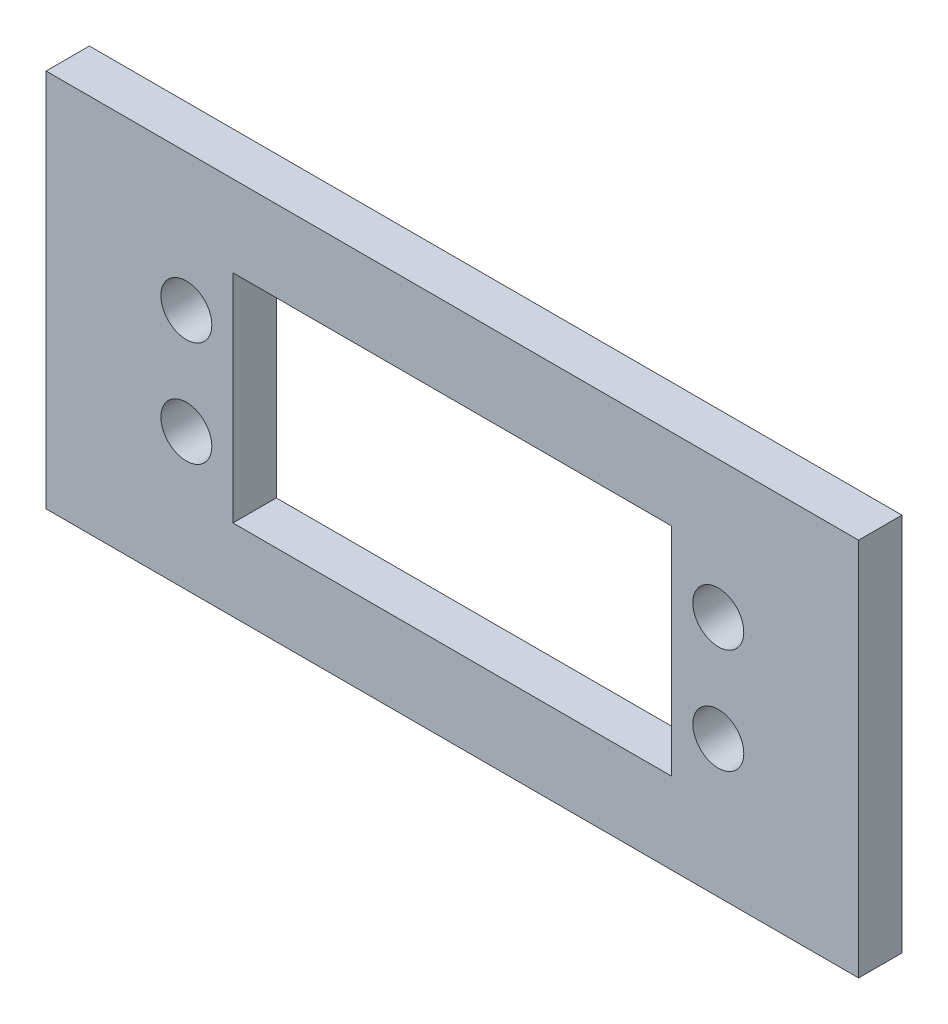
SolidWorks part; units mm, degrees
ref_plane "Front Plane" through (0, 0, 0) normal (0, 0, 1) x (1, 0, 0)
ref_plane "Top Plane" through (0, 0, 0) normal (0, 1, 0) x (1, 0, 0)
ref_plane "Right Plane" through (0, 0, 0) normal (1, 0, 0) x (0, 0, -1)
sketch "Sketch1" plane through (0, 0, 0) normal (0, 0, 1) x (1, 0, 0)
  line L5 (-24.55, 0) -> (-37.5, 0) construction
  line L6 (-24.55, 4.85) -> (24.55, 4.85) construction
  line L14 (-24.55, 4.85) -> (-24.55, -4.85) construction
  line L15 (-24.55, -4.85) -> (24.55, -4.85) construction
  line L16 (24.55, 4.85) -> (24.55, -4.85) construction
  line L17 (-24.55, 4.85) -> (24.55, -4.85) construction
  line L18 (-24.55, -4.85) -> (24.55, 4.85) construction
  line L19 (0, 4.85) -> (0, 32.122) construction
  line L20 (-20.25, 10) -> (20.25, 10)
  line L21 (-20.25, 10) -> (-20.25, -10)
  line L22 (-20.25, -10) -> (20.25, -10)
  line L23 (-37.5, 17.5) -> (37.5, 17.5)
  line L24 (-37.5, 17.5) -> (-37.5, -17.5)
  line L25 (20.25, 10) -> (20.25, -10)
  line L26 (-20.25, 10) -> (20.25, -10) construction
  line L27 (-20.25, -10) -> (20.25, 10) construction
  line L28 (0, 32.122) -> (0, 32.2159) construction
  line L29 (-37.5, -17.5) -> (37.5, -17.5)
  line L30 (37.5, 17.5) -> (37.5, -17.5)
  line L31 (-37.5, 17.5) -> (37.5, -17.5) construction
  line L32 (-37.5, -17.5) -> (37.5, 17.5) construction
  circle A4 centre (-24.55, 4.85) radius 2.35
  circle A5 centre (-24.55, -4.85) radius 2.35
  circle A6 centre (24.55, -4.85) radius 2.35
  circle A7 centre (24.55, 4.85) radius 2.35
  point P0 (-24.55, 4.85)
  point P1 (-24.55, -4.85)
  point P3 (24.55, -4.85)
  point P5 (24.55, 4.85)
  point P12 (0, 0)
  point P22 (0, 0)
  point P28 (0, 0)
  point P29 (0, 0)
  dimension "D3" = 4.7
  dimension "D1" = 49.1
  dimension "D2" = 9.7
  dimension "D4" = 40.5
  dimension "D5" = 20
  dimension "D6" = 75
  dimension "D7" = 35
extrude "Boss-Extrude1" add sketch "Sketch1" along normal blind 4
